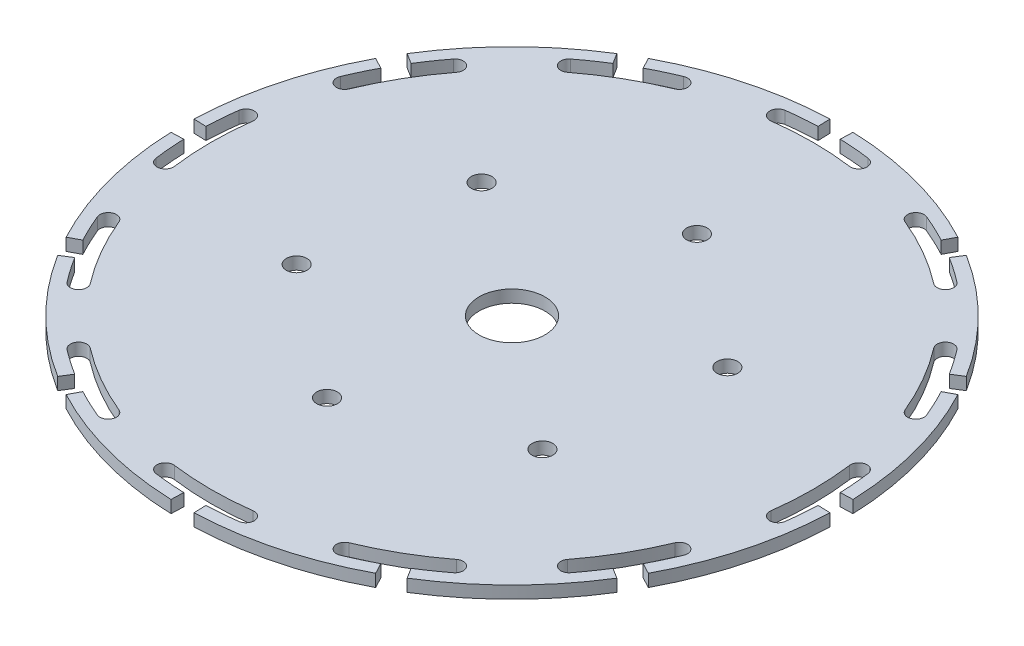
SolidWorks part; units mm, degrees
material "6061 Alloy"
ref_plane "Front Plane" through (0, 0, 0) normal (0, 0, 1) x (1, 0, 0)
ref_plane "Top Plane" through (0, 0, 0) normal (0, 1, 0) x (1, 0, 0)
ref_plane "Right Plane" through (0, 0, 0) normal (1, 0, 0) x (0, 0, -1)
sketch "Sketch1" plane through (0, 0, 0) normal (0, 1, 0) x (1, 0, 0)
  circle A0 centre (0, 0) radius 40
  dimension "D1" = 80
sketch "Sketch2" plane through (0, 0, 0) normal (0, 1, 0) x (1, 0, 0)
  line L0 (0, 0) -> (0, 40) construction
  line L1 (-1.396, 39.9756) -> (0, 0) construction
  line L2 (0, 0) -> (-5.221, 39.6578) construction
  line L3 (-1.396, 39.9756) -> (-1.3436, 38.4765)
  line L4 (0, 0) -> (5.221, 39.6578) construction
  line L5 (1.396, 39.9756) -> (0, 0) construction
  line L6 (1.396, 39.9756) -> (1.3436, 38.4765)
  arc A0 (4.7642, 36.1877) -> (-4.7642, 36.1877) centre (0, 0) ccw
  circle A1 centre (0, 0) radius 40 construction
  arc A2 (-1.396, 39.9756) -> (1.396, 39.9756) centre (0, 0) cw
  arc A3 (-1.3436, 38.4765) -> (-5.0253, 38.1706) centre (0, 0) ccw
  arc A4 (-4.7642, 36.1877) -> (-5.0253, 38.1706) centre (-4.8947, 37.1792) cw
  arc A5 (4.7642, 36.1877) -> (5.0253, 38.1706) centre (4.8947, 37.1792) ccw
  arc A6 (1.3436, 38.4765) -> (5.0253, 38.1706) centre (0, 0) cw
  point P130 (0, 0)
  dimension "D1" = 15
  dimension "D2" = 2
  dimension "D4" = 1.5
  dimension "D3" = 4
sketch "Sketch3" plane through (0, 0, 0) normal (0, 1, 0) x (1, 0, 0)
  circle A0 centre (0, 0) radius 4
  dimension "D1" = 8
extrude "Wheel Blank" add sketch "Sketch1" along normal blind 1.5
extrude "T-Slot" cut sketch "Sketch2" along normal through all
pattern_circular "CirPattern" count 12 over 360 about axis through (0, 0, 0) along (0, 1, 0) of "T-Slot"
extrude "Center Hole" cut sketch "Sketch3" along normal blind 6
hole_wizard "M3 Clearance Hole1" positions "Sketch5" profile "Sketch4" hole size "M3" standard "ISO"
sketch "Sketch5" plane through (0, 1.5, 0) normal (0, 1, 0) x (1, 0, 0)
  line L0 (4.8947, 37.1792) -> (0, 0) construction
  point P8 (2.6105, 19.8289)
  dimension "D1" = 20
sketch "Sketch4" plane through (2.6105, 1.5, -19.8289) normal (1, 0, 0) x (0, 0, 1)
  line L0 (0, 0) -> (0, 10.7511)
  line L1 (0, 10.7511) -> (1.25, 10)
  line L2 (1.25, 10) -> (1.25, 0)
  line L5 (1.25, 0) -> (0, 0)
  line L10 (0, 10.7511) -> (-1.25, 10) construction
  line L11 (0, -6.35) -> (0, 107.95) construction
  dimension "Hole Dia." = 2.5
  dimension "Hole Depth" = 10
  dimension "Drill Angle" = 118
pattern_circular "CirPattern1" count 6 over 360 about axis through (0, 0, 0) along (0, 1, 0) of "M3 Clearance Hole1"
